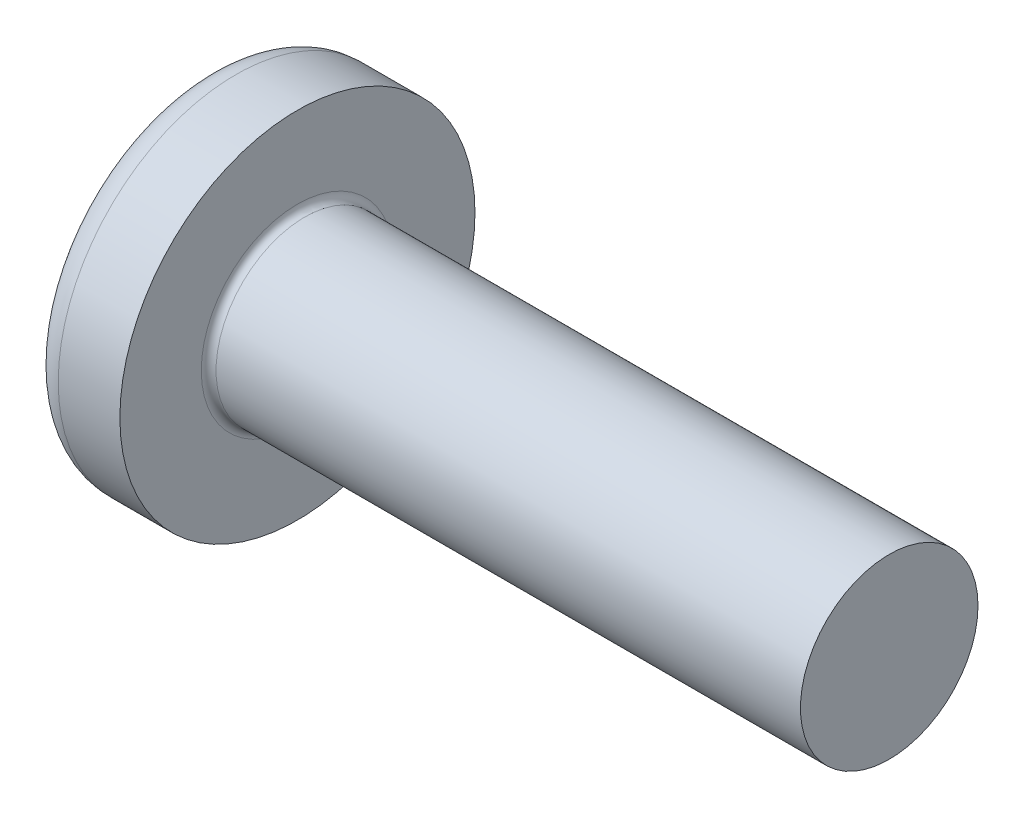
SolidWorks part; units mm, degrees
ref_plane "Front" through (0, 0, 0) normal (0, 0, 1) x (1, 0, 0)
ref_plane "Top" through (0, 0, 0) normal (0, 1, 0) x (1, 0, 0)
ref_plane "Right" through (0, 0, 0) normal (1, 0, 0) x (0, 0, -1)
sketch "Sketch1" plane through (0, 0, 0) normal (1, 0, 0) x (0, 0, -1)
  circle A0 centre (0, 0) radius 6
  dimension "dk" = 12
extrude "BaseHead" add sketch "Sketch1" along normal blind 4.6
sketch "Sketch2" plane through (4.6, 0, 0) normal (1, 0, 0) x (0, 0, -1)
  circle A0 centre (0, 0) radius 3
  dimension "d" = 6
extrude "BaseBody" add sketch "Sketch2" along normal blind 20
cosmetic thread "ThreadCosmetic1" [suppressed] parameters "D1"=20, "THD_MINOR"=4.917
fillet "Fillet1" radius 0.25 1 edges at (4.6, 0, -3)
sketch "Sketch3" plane through (-4.0827, -1.9173, 0) normal (0, 0, 1) x (0, -1, 0)
  line L0 (-1.9173, 6.3195) -> (-1.9173, 20.448) construction
  line L3 (-7.9173, 4.0827) -> (-1.9173, 4.0827) construction
  line L5 (-7.9173, 6.0827) -> (-7.9173, -0.9173)
  line L6 (-1.9173, 4.0827) -> (-1.9173, -0.9173)
  line L7 (-1.9173, -0.9173) -> (-7.9173, -0.9173)
  line L8 (-7.9173, 8.6827) -> (-7.9173, 4.0827) construction
  arc A0 (-7.9173, 6.0827) -> (-1.9173, 4.0827) centre (-1.9173, 14.0827) ccw
  dimension "r1" = 10
  dimension "D2" = 5
revolve "BaseTop" cut sketch "Sketch3" angle 360 about L0
sketch "Sketch4" plane through (0, 0, 0) normal (1, 0, 0) x (0, 0, -1)
  line L1 (2.396, 0) -> (1.198, 2.075)
  line L2 (1.198, 2.075) -> (-1.198, 2.075)
  line L3 (-1.198, 2.075) -> (-2.396, 0)
  line L4 (-2.396, 0) -> (-1.198, -2.075)
  line L5 (-1.198, -2.075) -> (1.198, -2.075)
  line L6 (1.198, -2.075) -> (2.396, 0)
  circle A0 centre (0, 0) radius 2.075 construction
  dimension "B" = 4.15
extrude "Socket" cut sketch "Sketch4" along normal blind 2
sketch "Sketch5" plane through (2, 0, 0) normal (-1, 0, 0) x (0, 0, 1)
  line L0 (2.396, 0) -> (1.198, -2.075) construction
  line L1 (1.198, 2.075) -> (2.396, 0) construction
  line L2 (1.198, -2.075) -> (-1.198, -2.075) construction
  line L3 (-1.198, -2.075) -> (-2.396, 0) construction
  line L4 (-1.198, 2.075) -> (1.198, 2.075) construction
  line L5 (-2.396, 0) -> (-1.198, 2.075) construction
  line L6 (2.396, 0) -> (1.198, -2.075)
  line L7 (1.198, 2.075) -> (2.396, 0)
  line L8 (1.198, -2.075) -> (-1.198, -2.075)
  line L9 (-1.198, -2.075) -> (-2.396, 0)
  line L10 (-1.198, 2.075) -> (1.198, 2.075)
  line L11 (-2.396, 0) -> (-1.198, 2.075)
extrude "Cut-Extrude2" cut sketch "Sketch5" against normal blind 5 draft 60
sketch "Sketch6" plane through (-30.7487, 13.2487, 0) normal (0, 0, 1) x (0, -1, 0)
  line L0 (13.2487, 89.8637) -> (13.2487, 24.8312) construction
  line L1 (-4.2098, 35.3487) -> (10.5402, 35.3487)
  line L2 (-4.2098, 35.3487) -> (-4.2098, 17.3487)
  line L3 (-4.2098, 17.3487) -> (10.2487, 17.3487)
  line L4 (10.7902, 35.5987) -> (10.7902, 14.8487)
  line L5 (10.5402, 35.3487) -> (10.7902, 35.3487)
  line L6 (10.2487, 17.3487) -> (10.7902, 14.8487)
  line L7 (10.7902, 35.5987) -> (10.7902, 35.3487)
  line L8 (16.2487, 55.3487) -> (10.2487, 55.3487) construction
  line L9 (19.2487, 35.3487) -> (7.2487, 35.3487) construction
  arc A0 (10.5402, 35.3487) -> (10.7902, 35.5987) centre (10.5402, 35.5987) ccw construction
  dimension "d1" = 4.917
  dimension "D2" = 15
  dimension "b" = 38
  dimension "x" = 2.5
  dimension "d" = 6
  dimension "r" = 0.25
fillet "HeadFillet2" radius 1 1 edges at (2, 0, 6)
sketch "Sketch8" plane through (0, 0, 0) normal (0, 0, 1) x (1, 0, 0)
  line L0 (24.6, 2.531) -> (24.8708, 3)
  line L1 (24.8708, 3) -> (24.8708, 3.5415)
  line L2 (24.8708, 3.5415) -> (24.3293, 3.5415)
  line L3 (24.3293, 3.5415) -> (24.3293, 3)
  line L4 (24.3293, 3) -> (24.6, 2.531)
  line L5 (24.6, -3) -> (24.6, 3) construction
  line L6 (0, 0) -> (27.6816, 0) construction
  dimension "D1" = 0.5415
  dimension "D2" = 6
revolve "Cut-Revolve10" [suppressed] cut sketch "Sketch8" angle 360 about L6
pattern_linear "LPattern10" [suppressed] count 31 spacing 0.6498 along (1, 0, 0)
equation "\"D2@Sketch8\" = \"d@Sketch2\""
equation "\"D1@Sketch8\" =  ( \"d@Sketch2\" - \"THD_MINOR@ThreadCosmetic1\" )  / 2"
equation "\"D3@LPattern10\" = \"D1@Sketch8\" * 1.2"
equation "\"D1@LPattern10\" = \"D1@ThreadCosmetic1\" / \"D3@LPattern10\" "
